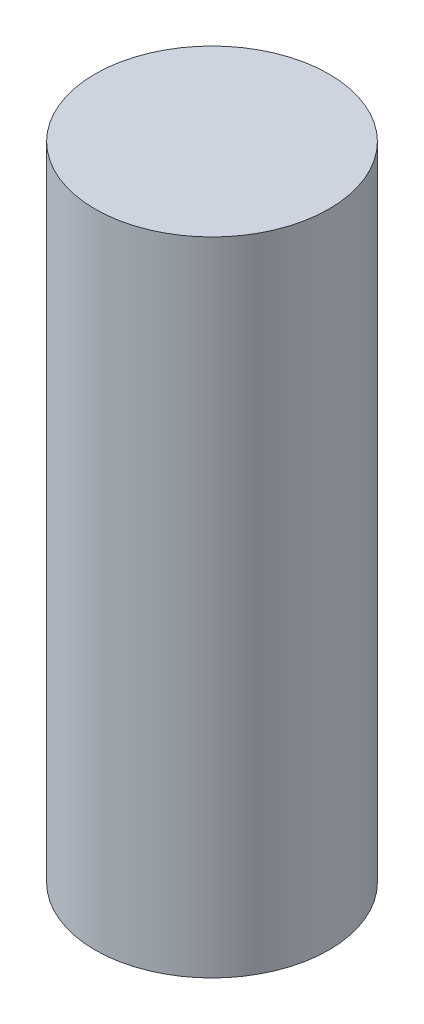
SolidWorks part; units mm, degrees
ref_plane "Front Plane" through (0, 0, 0) normal (0, 0, 1) x (1, 0, 0)
ref_plane "Top Plane" through (0, 0, 0) normal (0, 1, 0) x (1, 0, 0)
ref_plane "Right Plane" through (0, 0, 0) normal (1, 0, 0) x (0, 0, -1)
sketch "Sketch1" plane through (0, 0, 0) normal (0, 1, 0) x (1, 0, 0)
  circle A0 centre (0, 0) radius 69.723
  dimension "D1" = 139.446
extrude "Boss-Extrude1" add sketch "Sketch1" along normal blind 382.524
